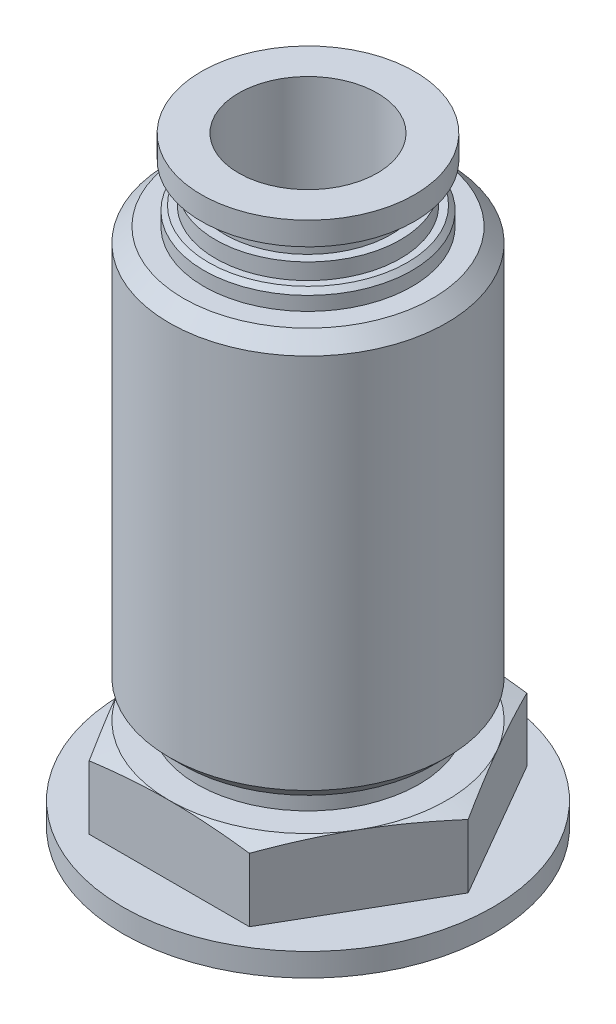
SolidWorks part; units mm, degrees
ref_plane "Front" through (0, 0, 0) normal (0, 0, 1) x (1, 0, 0)
ref_plane "Top" through (0, 0, 0) normal (0, 1, 0) x (1, 0, 0)
ref_plane "Right" through (0, 0, 0) normal (1, 0, 0) x (0, 0, -1)
ref_plane "Plane1" through (0, 0, 0) normal (0, 0, 1) x (1, 0, 0)
sketch "Sketch1" plane through (0, 0, 0) normal (0, 0, 1) x (1, 0, 0)
  line L0 (0, 34) -> (4.6154, 34)
  line L1 (4.6154, 34) -> (4.6154, 33)
  line L2 (4.6154, 33) -> (3.6, 33)
  line L3 (3.6, 33) -> (3.6, 32)
  line L4 (3.6, 32) -> (4, 32)
  line L5 (4, 32) -> (4, 12)
  line L6 (4, 12) -> (4.8, 12)
  line L7 (4.8, 12) -> (4.8, 9.5)
  line L8 (4.8, 9.5) -> (3.1579, 9.5)
  line L9 (3.1579, 9.5) -> (3.1579, 8)
  line L10 (3.1579, 8) -> (0, 8)
  line L11 (0, 8) -> (0, 34)
  line L12 (0, 8) -> (0, 34) construction
revolve "Revolve1" add sketch "Sketch1" angle 360 about L12
ref_plane "Plane2" through (0, 0, 0) normal (0, 0, 1) x (1, 0, 0)
sketch "Sketch2" plane through (0, 0, 0) normal (0, 0, 1) x (1, 0, 0)
  line L0 (0, 30.5) -> (5.3865, 30.5)
  line L1 (5.3865, 30.5) -> (6, 29.8865)
  line L2 (6, 29.8865) -> (6, 13.6135)
  line L3 (6, 13.6135) -> (5.3865, 13)
  line L4 (5.3865, 13) -> (0, 13)
  line L5 (0, 13) -> (0, 30.5)
  line L6 (0, 13) -> (0, 30.5) construction
revolve "Revolve2" add sketch "Sketch2" angle 360 about L6
ref_plane "Plane3" through (0, 0, 0) normal (0, 0, 1) x (1, 0, 0)
sketch "Sketch3" plane through (0, 0, 0) normal (0, 0, 1) x (1, 0, 0)
  line L0 (0, 32) -> (3.5, 32)
  line L1 (3.5, 32) -> (4, 31.3)
  line L2 (4, 31.3) -> (4.3, 31.3)
  line L3 (4.3, 31.3) -> (4.5, 31.1)
  line L4 (4.5, 31.1) -> (4.5, 30.5)
  line L5 (4.5, 30.5) -> (0, 30.5)
  line L6 (0, 30.5) -> (0, 32)
  line L7 (0, 30.5) -> (0, 32) construction
revolve "Revolve3" add sketch "Sketch3" angle 360 about L7
ref_plane "Plane4" through (0, 0, 0) normal (0, 0, 1) x (1, 0, 0)
sketch "Sketch4" plane through (0, 0, 0) normal (0, 0, 1) x (1, 0, 0)
  line L0 (0, 12) -> (6, 12)
  line L1 (6, 12) -> (7.2, 11.6785)
  line L2 (7.2, 11.6785) -> (7.2, 9)
  line L3 (7.2, 9) -> (8, 9)
  line L4 (8, 9) -> (8, 8)
  line L5 (8, 8) -> (0, 8)
  line L6 (0, 8) -> (0, 12)
  line L7 (0, 8) -> (0, 12) construction
revolve "Revolve4" add sketch "Sketch4" angle 360 about L7
ref_plane "Plane5" through (0, 12, 0) normal (0, 1, 0) x (-1, 0, 0)
sketch "Sketch5" plane through (0, 12, 0) normal (0, 1, 0) x (-1, 0, 0)
  line L0 (17, 17) -> (-17, 17)
  line L1 (-17, 17) -> (-17, -17)
  line L2 (-17, -17) -> (17, -17)
  line L3 (17, -17) -> (17, 17)
  line L4 (6.9282, 0) -> (3.4641, 6)
  line L5 (3.4641, 6) -> (-3.4641, 6)
  line L6 (-3.4641, 6) -> (-6.9282, 0)
  line L7 (-6.9282, 0) -> (-3.4641, -6)
  line L8 (-3.4641, -6) -> (3.4641, -6)
  line L9 (3.4641, -6) -> (6.9282, 0)
extrude "Cut-Extrude1" cut sketch "Sketch5" against normal blind 3
ref_plane "Plane6" through (0, 0, 0) normal (0, 0, 1) x (1, 0, 0)
sketch "Sketch6" plane through (0, 0, 0) normal (0, 0, 1) x (1, 0, 0)
  line L0 (0, 34) -> (3, 34)
  line L1 (3, 34) -> (3, 22.3)
  line L2 (3, 22.3) -> (0, 22.3)
  line L3 (0, 22.3) -> (0, 34)
  line L4 (0, 22.3) -> (0, 34) construction
revolve "Cut-Revolve1" cut sketch "Sketch6" angle 360 about L4
ref_plane "Plane7" through (0, 0, 0) normal (0, 0, 1) x (1, 0, 0)
sketch "Sketch7" plane through (0, 0, 0) normal (0, 0, 1) x (1, 0, 0)
  line L0 (0, 13) -> (4.8, 13)
  line L1 (4.8, 13) -> (4.8, 12)
  line L2 (4.8, 12) -> (0, 12)
  line L3 (0, 12) -> (0, 13)
  line L4 (0, 12) -> (0, 13) construction
revolve "Revolve5" add sketch "Sketch7" angle 360 about L4
